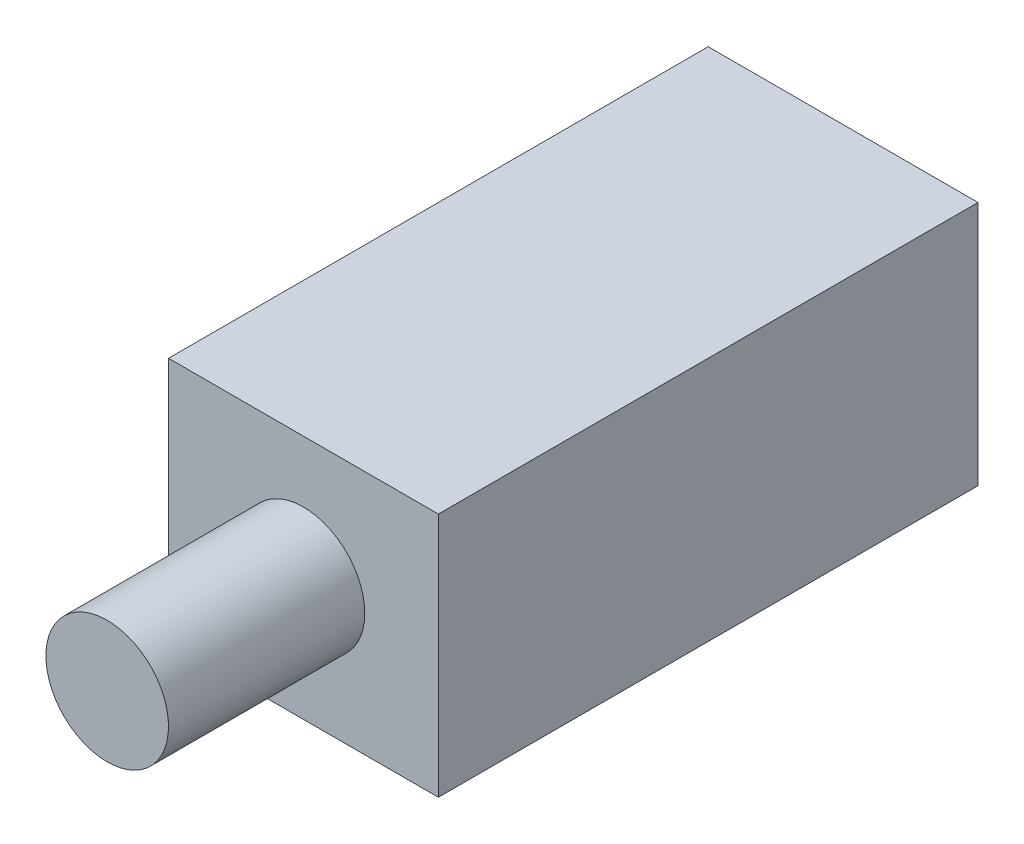
SolidWorks part; units mm, degrees
material "Aluminium"
ref_plane "Ebene vorne" through (0, 0, 0) normal (0, 0, 1) x (1, 0, 0)
ref_plane "Ebene oben" through (0, 0, 0) normal (0, 1, 0) x (1, 0, 0)
ref_plane "Ebene rechts" through (0, 0, 0) normal (1, 0, 0) x (0, 0, -1)
sketch "Skizze1" plane through (0, 0, 0) normal (0, 0, 1) x (1, 0, 0)
  line L1 (-5.5, 10) -> (5.5, 10)
  line L2 (-5.5, 10) -> (-5.5, 0)
  line L3 (-5.5, 0) -> (5.5, 0)
  line L4 (5.5, 10) -> (5.5, 0)
  dimension "D1" = 11
  dimension "D2" = 10
extrude "Linear austragen1" add sketch "Skizze1" against normal blind 22
sketch "Skizze2" plane through (0, 0, 0) normal (0, 0, 1) x (1, 0, 0)
  line L0 (0, 0) -> (0, 5) construction
  line L1 (-5.5, 0) -> (5.5, 0) construction
  line L2 (0, 5) -> (5.5, 5) construction
  line L3 (5.5, 0) -> (5.5, 10) construction
  circle A0 centre (0, 5) radius 2.5
  dimension "D1" = 5
extrude "Linear austragen2" add sketch "Skizze2" along normal blind 8
